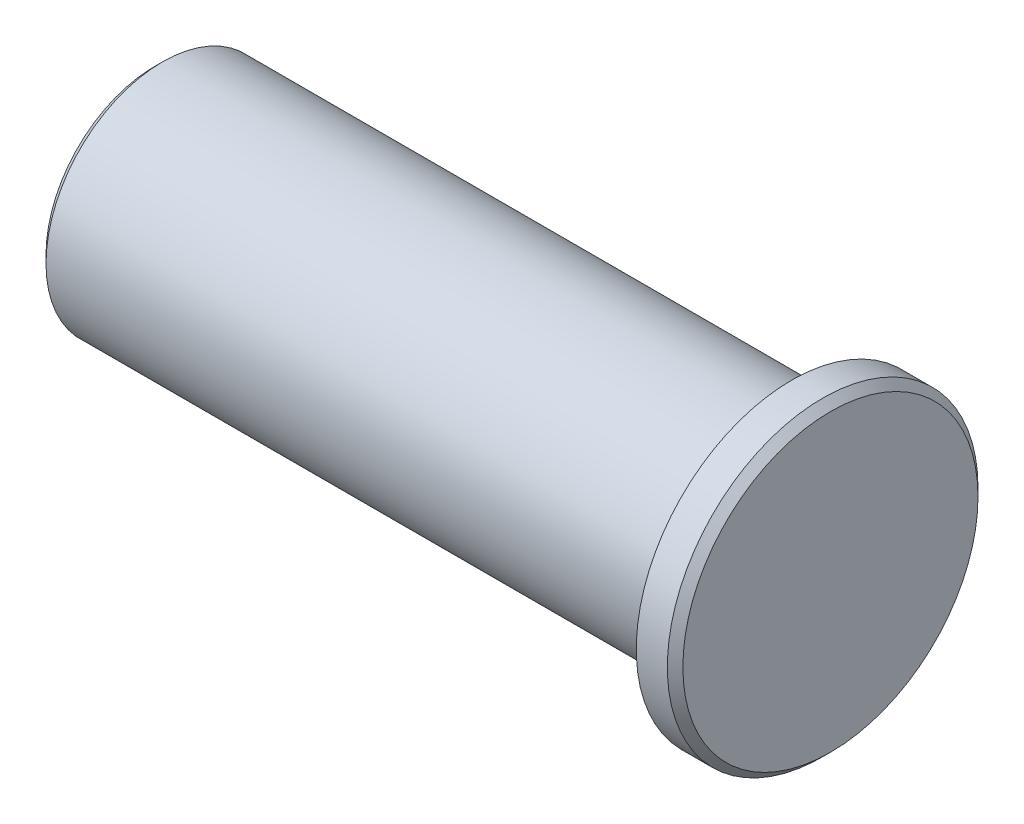
SolidWorks part; units mm, degrees
material "AISI 1045 钢，冷拔"
ref_plane "前视基准面" through (0, 0, 0) normal (0, 0, 1) x (1, 0, 0)
ref_plane "上视基准面" through (0, 0, 0) normal (0, 1, 0) x (1, 0, 0)
ref_plane "右视基准面" through (0, 0, 0) normal (1, 0, 0) x (0, 0, -1)
sketch "草图1" plane through (0, 0, 0) normal (1, 0, 0) x (0, 0, -1)
  circle A0 centre (0, 0) radius 15
  dimension "D1" = 30
extrude "凸台-拉伸1" add sketch "草图1" along normal blind 82
sketch "草图2" plane through (82, 0, 0) normal (1, 0, 0) x (0, 0, -1)
  circle A0 centre (0, 0) radius 20
  dimension "D1" = 40
extrude "凸台-拉伸2" add sketch "草图2" along normal blind 5
chamfer "倒角1" distance 1 angle 45 2 edges at (0, 0, -15) (87, 0, -20)
hole_wizard "M8 螺纹孔的螺纹孔钻头1" positions "3D草图1" profile "草图3" hole size "M8" standard "GB"
sketch3d "3D草图1"
  point P0 (0, 0, 0)
  point P3 (0, 0, 0)
sketch "草图3" plane through (0, 0, 0) normal (0, 1, 0) x (0, 0, 1)
  line L0 (0, 0) -> (0, 17.0429)
  line L1 (0, 17.0429) -> (3.4, 15)
  line L2 (3.4, 15) -> (3.4, 0)
  line L5 (3.4, 0) -> (0, 0)
  line L10 (0, 17.0429) -> (-3.4, 15) construction
  line L11 (0, -6.35) -> (0, 107.95) construction
  dimension "孔直径" = 6.8
  dimension "孔深度" = 15
  dimension "导头角度" = 118
